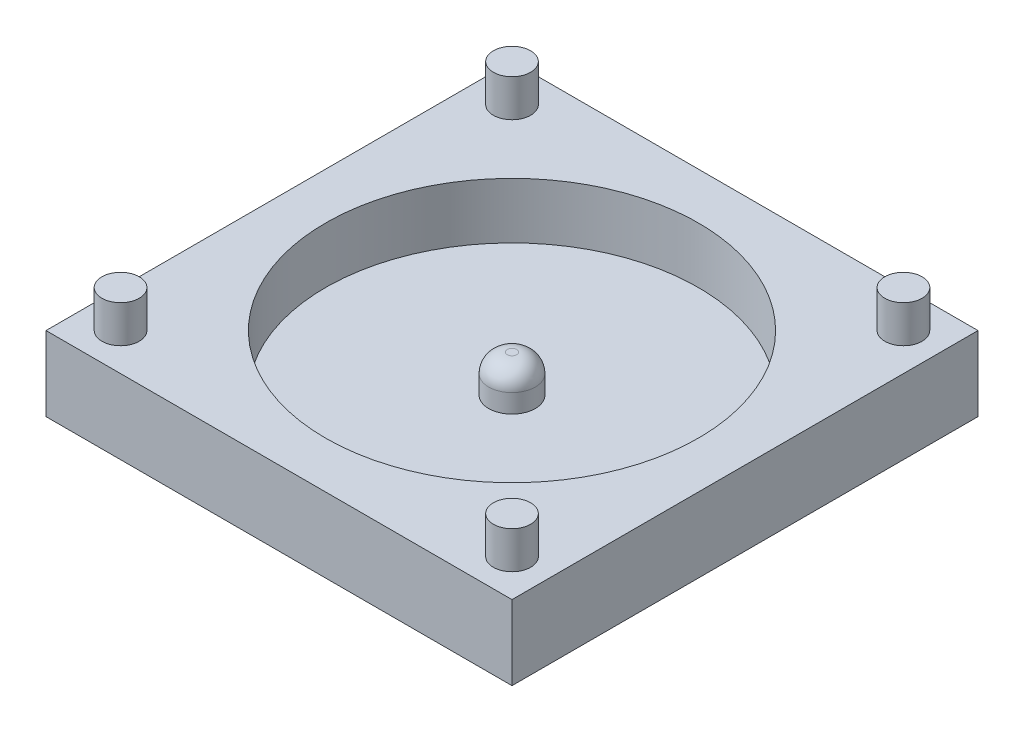
SolidWorks part; units mm, degrees
ref_plane "Front Plane" through (0, 0, 0) normal (0, 0, 1) x (1, 0, 0)
ref_plane "Top Plane" through (0, 0, 0) normal (0, 1, 0) x (1, 0, 0)
ref_plane "Right Plane" through (0, 0, 0) normal (1, 0, 0) x (0, 0, -1)
sketch "Sketch1" plane through (0, 0, 0) normal (0, 1, 0) x (1, 0, 0)
  line L1 (-12.5, -12.5) -> (12.5, -12.5)
  line L2 (-12.5, -12.5) -> (-12.5, 12.5)
  line L3 (-12.5, 12.5) -> (12.5, 12.5)
  line L4 (12.5, -12.5) -> (12.5, 12.5)
  line L5 (-12.5, -12.5) -> (12.5, 12.5) construction
  line L6 (-12.5, 12.5) -> (12.5, -12.5) construction
  point P0 (0, 0)
  dimension "D1" = 25
  dimension "D2" = 25
extrude "Boss-Extrude1" add sketch "Sketch1" along normal blind 4
sketch "Sketch2" plane through (0, 4, 0) normal (0, 1, 0) x (1, 0, 0)
  circle A0 centre (0, 0) radius 10
  dimension "D1" = 20
extrude "Cut-Extrude1" cut sketch "Sketch2" against normal blind 3
sketch "Sketch3" plane through (0, 1, 0) normal (0, 1, 0) x (1, 0, 0)
  circle A0 centre (0, 0) radius 1.25
  dimension "D1" = 2.5
extrude "Boss-Extrude2" add sketch "Sketch3" along normal blind 2
fillet "Fillet1" radius 1 1 edges at (0, 3, 1.25)
sketch "Sketch4" plane through (0, 4, 0) normal (0, 1, 0) x (1, 0, 0)
  line L0 (12.5, 12.5) -> (-12.5, 12.5) construction
  line L1 (-12.5, 12.5) -> (-12.5, -12.5) construction
  line L2 (-12.5, -12.5) -> (12.5, -12.5) construction
  line L3 (12.5, -12.5) -> (12.5, 12.5) construction
  circle A0 centre (-10.5, 10.5) radius 1
  circle A1 centre (10.5, 10.5) radius 1
  circle A2 centre (10.5, -10.5) radius 1
  circle A3 centre (-10.5, -10.5) radius 1
  dimension "D1" = 2
  dimension "D4" = 2
  dimension "D7" = 2
  dimension "D10" = 2
  dimension "D2" = 2
  dimension "D3" = 2
  dimension "D5" = 2
  dimension "D6" = 2
  dimension "D8" = 2
  dimension "D9" = 2
  dimension "D11" = 2
  dimension "D12" = 2
extrude "Boss-Extrude3" add sketch "Sketch4" along normal blind 2
